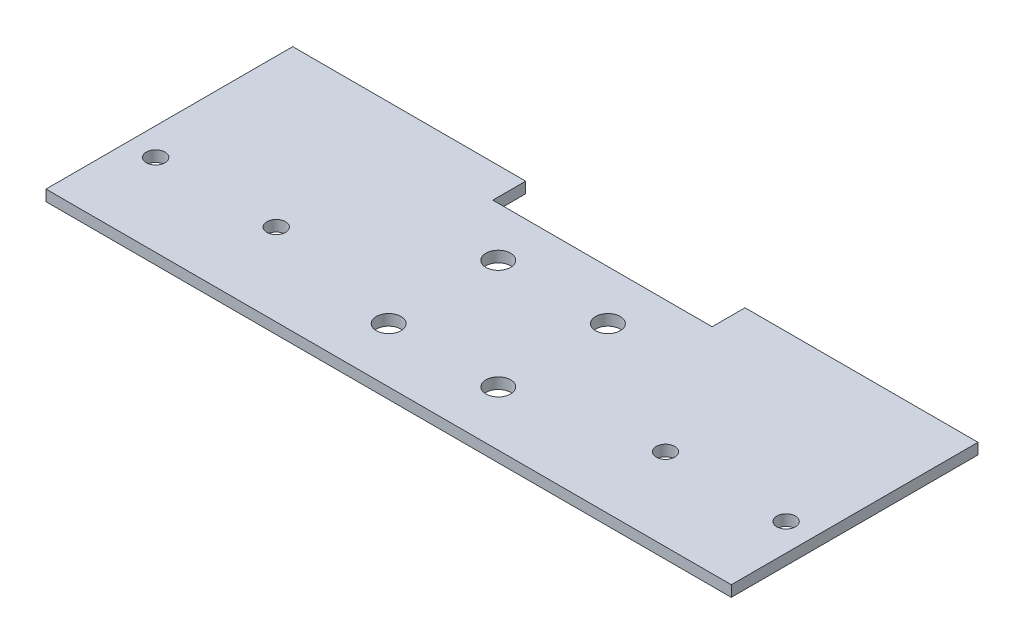
SolidWorks part; units mm, degrees
ref_plane "Front Plane" through (0, 0, 0) normal (0, 0, 1) x (1, 0, 0)
ref_plane "Top Plane" through (0, 0, 0) normal (0, 1, 0) x (1, 0, 0)
ref_plane "Right Plane" through (0, 0, 0) normal (1, 0, 0) x (0, 0, -1)
sketch "Sketch1" plane through (0, 0, 0) normal (0, 1, 0) x (1, 0, 0)
  line L1 (-62.5, -22.5) -> (62.5, -22.5)
  line L2 (-62.5, -22.5) -> (-62.5, 22.5)
  line L3 (-62.5, 22.5) -> (62.5, 22.5)
  line L4 (62.5, -22.5) -> (62.5, 22.5)
  line L5 (-62.5, -22.5) -> (62.5, 22.5) construction
  line L6 (-62.5, 22.5) -> (62.5, -22.5) construction
  point P0 (0, 0)
  dimension "D1" = 45
  dimension "D2" = 125
extrude "Boss-Extrude1" add sketch "Sketch1" along normal blind 2
sketch "Sketch2" plane through (0, 2, 0) normal (0, 1, 0) x (1, 0, 0)
  line L1 (-10, -12.5) -> (10, -12.5) construction
  line L5 (-10, 7.5) -> (10, 7.5) construction
  line L6 (-10, 7.5) -> (-10, -12.5) construction
  line L11 (0, 17.5) -> (0, -22.5) construction
  line L12 (-62.5, -22.5) -> (62.5, -22.5) construction
  line L13 (-10, -12.5) -> (10, -12.5) construction
  line L14 (10, 7.5) -> (10, -12.5) construction
  line L15 (-10, 7.5) -> (10, -12.5) construction
  line L16 (-10, -12.5) -> (10, 7.5) construction
  circle A2 centre (-10, -12.5) radius 2.25
  circle A3 centre (10, -12.5) radius 2.25
  circle A4 centre (-10, 7.5) radius 2.25
  circle A5 centre (10, 7.5) radius 2.25
  point P0 (0, -2.5)
  point P6 (0, -12.5)
  point P9 (-10, -12.5)
  point P10 (10, -12.5)
  dimension "D6" = 4.5
  dimension "D5" = 4.5
  dimension "D3" = 4.5
  dimension "D4" = 4.5
  dimension "D9" = 10
  dimension "D1" = 20
  dimension "D2" = 20
extrude "Cut-Extrude1" cut sketch "Sketch2" against normal blind 10
sketch "Sketch3" plane through (0, 2, 0) normal (0, 1, 0) x (1, 0, 0)
  circle A0 centre (57.5, -7.5) radius 1.7 construction
  circle A1 centre (35.5, -7.5) radius 1.7 construction
  circle A2 centre (-35.5047, -7.5) radius 1.7 construction
  circle A3 centre (-57.5, -7.5) radius 1.7 construction
  circle A4 centre (57.5, -7.5) radius 1.7
  circle A5 centre (35.5, -7.5) radius 1.7
  circle A6 centre (-35.5047, -7.5) radius 1.7
  circle A7 centre (-57.5, -7.5) radius 1.7
extrude "Cut-Extrude2" cut sketch "Sketch3" against normal blind 10
sketch "Sketch4" plane through (0, 2, 0) normal (0, 1, 0) x (1, 0, 0)
  line L2 (62.5, 22.5) -> (-62.5, 22.5) construction
  line L3 (-20, 22.5) -> (20, 22.5)
  line L4 (-20, 22.5) -> (-20, 16.5)
  line L5 (-20, 16.5) -> (20, 16.5)
  line L6 (20, 22.5) -> (20, 16.5)
  line L7 (0, 0) -> (0, 22.5) construction
  dimension "D1" = 6
  dimension "D2" = 40
extrude "Cut-Extrude3" cut sketch "Sketch4" against normal blind 10
equation "\"D6@Sketch2\"=\"D5@Sketch2\""
equation "\"D3@Sketch2\"=\"D5@Sketch2\""
equation "\"D4@Sketch2\"=\"D5@Sketch2\""
